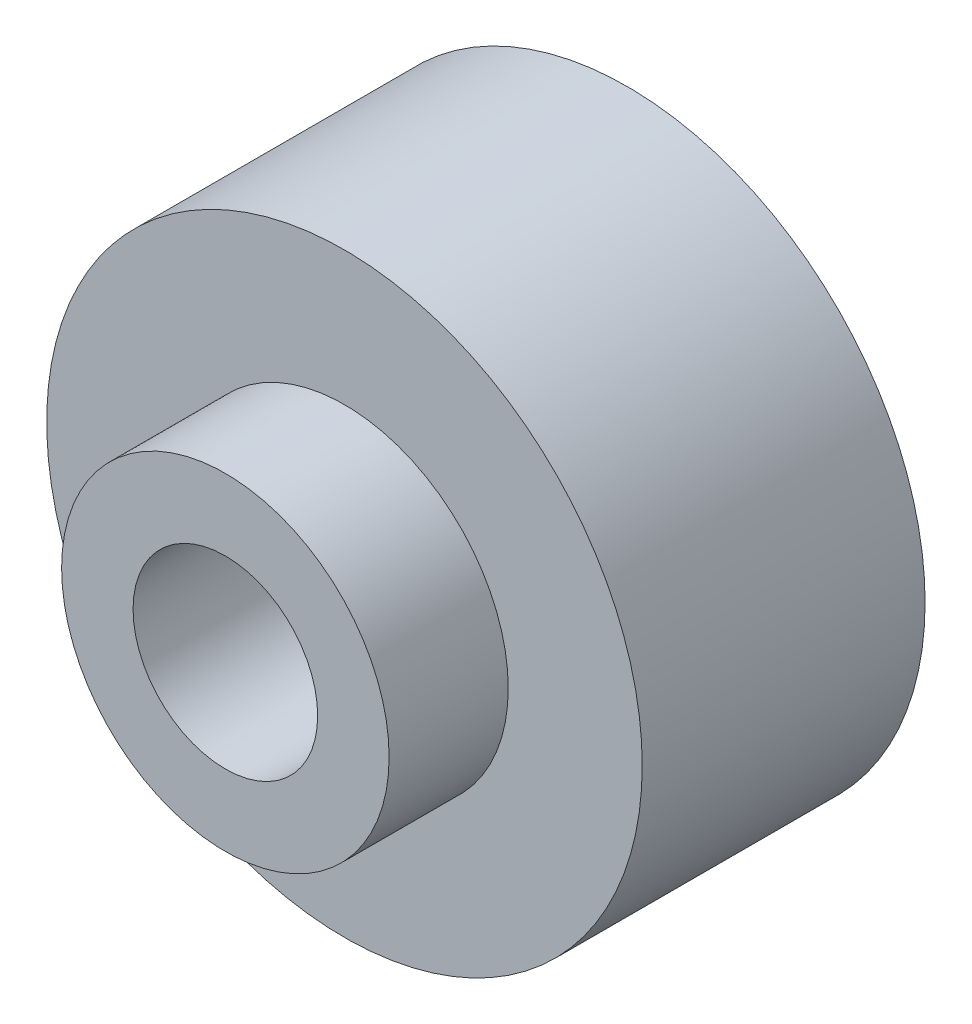
SolidWorks part; units mm, degrees
ref_plane "前视基准面" through (0, 0, 0) normal (0, 0, 1) x (1, 0, 0)
ref_plane "上视基准面" through (0, 0, 0) normal (0, 1, 0) x (1, 0, 0)
ref_plane "右视基准面" through (0, 0, 0) normal (1, 0, 0) x (0, 0, -1)
sketch "草图1" plane through (0, 0, 0) normal (0, 0, 1) x (1, 0, 0)
  circle A0 centre (0, 0) radius 5
  circle A1 centre (0, 0) radius 1.55
  dimension "D1" = 10
  dimension "D2" = 3.1
extrude "凸台-拉伸1" add sketch "草图1" along normal blind 4.75
sketch "草图2" plane through (0, 0, 4.75) normal (0, 0, 1) x (1, 0, 0)
  circle A0 centre (0, 0) radius 2.75
  circle A1 centre (0, 0) radius 1.55
  dimension "D1" = 5.5
extrude "凸台-拉伸2" add sketch "草图2" along normal blind 2
sketch "草图3" plane through (0, 0, 0) normal (0, 0, -1) x (-1, 0, 0)
  circle A0 centre (0, 0) radius 1.55
  circle A1 centre (0, 0) radius 3.5
  dimension "D1" = 7
extrude "切除-拉伸1" cut sketch "草图3" against normal blind 2
